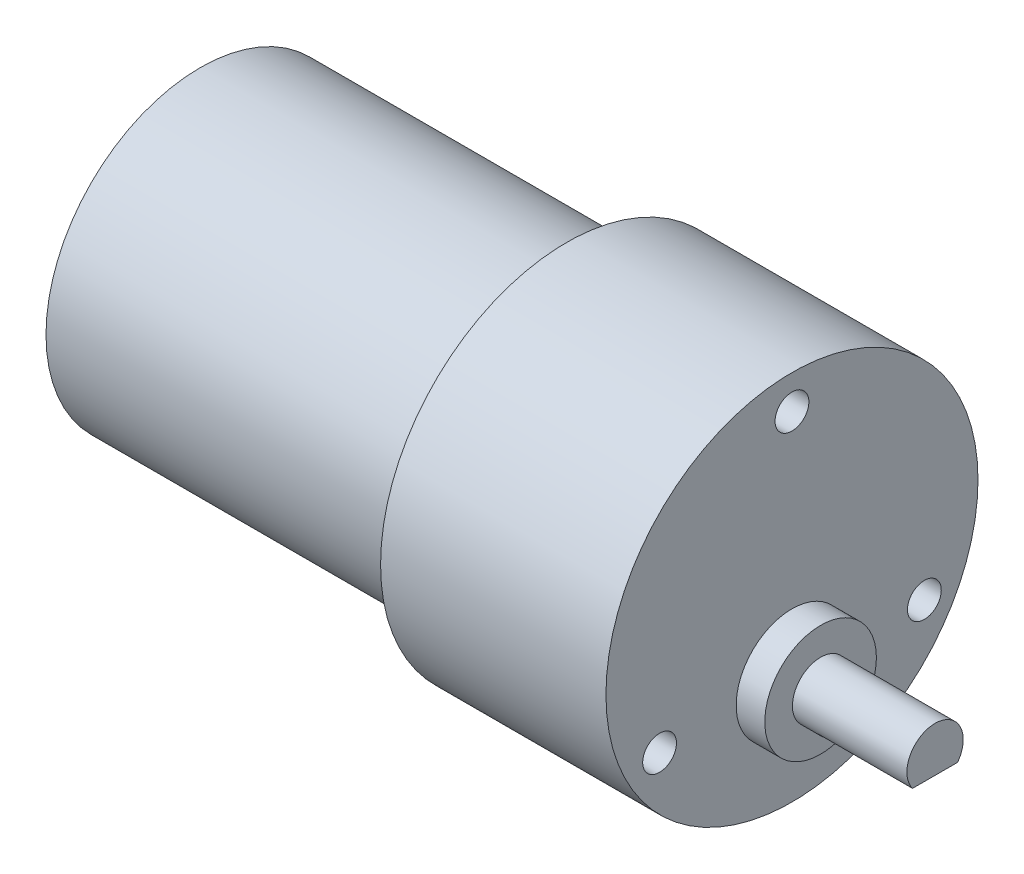
SolidWorks part; units mm, degrees
ref_plane "Front Plane" through (0, 0, 0) normal (0, 0, 1) x (1, 0, 0)
ref_plane "Top Plane" through (0, 0, 0) normal (0, 1, 0) x (1, 0, 0)
ref_plane "Right Plane" through (0, 0, 0) normal (1, 0, 0) x (0, 0, -1)
sketch "Sketch1" plane through (0, 0, 0) normal (1, 0, 0) x (0, 0, -1)
  circle A0 centre (0, 0) radius 16.51
  dimension "D1" = 33.02
extrude "Boss-Extrude2" add sketch "Sketch1" along normal blind 20
sketch "Sketch2" plane through (0, 0, 0) normal (-1, 0, 0) x (0, 0, 1)
  circle A0 centre (0, 0) radius 13.6906
  dimension "D1" = 27.3812
extrude "Boss-Extrude3" add sketch "Sketch2" along normal blind 32.512
sketch "Sketch3" plane through (20, 0, 0) normal (1, 0, 0) x (0, 0, -1)
  line L0 (0, -6.731) -> (0, -16.51) construction
  line L1 (0, 13.51) -> (0, 16.51) construction
  line L2 (11.75, -6.8416) -> (0, 13.51) construction
  line L3 (0, 13.51) -> (-11.75, -6.8416) construction
  line L4 (-11.75, -6.8416) -> (11.75, -6.8416) construction
  line L5 (0, -6.731) -> (11.75, -6.8416) construction
  line L6 (11.75, -6.8416) -> (0, -6.731) construction
  line L7 (0, -6.731) -> (-11.75, -6.8416) construction
  circle A1 centre (0, 0) radius 16.51 construction
  circle A2 centre (0, 13.51) radius 1.5
  circle A3 centre (11.75, -6.8416) radius 1.5
  circle A4 centre (-11.75, -6.8416) radius 1.5
  dimension "D3" = 3
  dimension "D7" = 3
  dimension "D8" = 3
  dimension "D4" = 3
  dimension "D5" = 23.5
  dimension "D6" = 23.5
  dimension "D9" = 23.5
extrude "Cut-Extrude1" cut sketch "Sketch3" against normal blind 6.35
sketch "Sketch4" plane through (20, 0, 0) normal (1, 0, 0) x (0, 0, -1)
  line L0 (0, -6.604) -> (0, -16.51) construction
  circle A0 centre (0, -6.604) radius 4.953
  circle A2 centre (0, 0) radius 16.51 construction
  dimension "D1" = 9.906
  dimension "D2" = 9.906
extrude "Boss-Extrude4" add sketch "Sketch4" along normal blind 2.54
sketch "Sketch5" plane through (22.54, 0, 0) normal (1, 0, 0) x (0, 0, -1)
  circle A0 centre (0, -6.604) radius 2.5
  dimension "D1" = 5
extrude "Boss-Extrude5" add sketch "Sketch5" along normal blind 10.16
sketch "Sketch6" plane through (-32.512, 0, 0) normal (-1, 0, 0) x (0, 0, 1)
  circle A0 centre (0, 0) radius 5
  dimension "D1" = 10
extrude "Boss-Extrude6" add sketch "Sketch6" along normal blind 2
sketch "Sketch7" plane through (-34.512, 0, 0) normal (-1, 0, 0) x (0, 0, 1)
  circle A0 centre (0, 0) radius 1.143
  dimension "D1" = 2.286
extrude "Boss-Extrude7" add sketch "Sketch7" along normal blind 3.048
sketch "Sketch8" plane through (32.7, 0, 0) normal (1, 0, 0) x (0, 0, -1)
  line L0 (0, -4.104) -> (0, -8.104) construction
  line L1 (0, -8.104) -> (2, -8.104)
  line L2 (2, -8.104) -> (-2, -8.104)
  circle A0 centre (0, -6.604) radius 2.5 construction
  circle A1 centre (0, -6.604) radius 2.5 construction
  arc A2 (-2, -8.104) -> (2, -8.104) centre (0, -6.604) ccw
  circle M1 centre (0, -6.604) radius 2.5
  dimension "D1" = 4
extrude "Cut-Extrude2" cut sketch "Sketch8" against normal blind 8.382 contours L1 L2 M1
